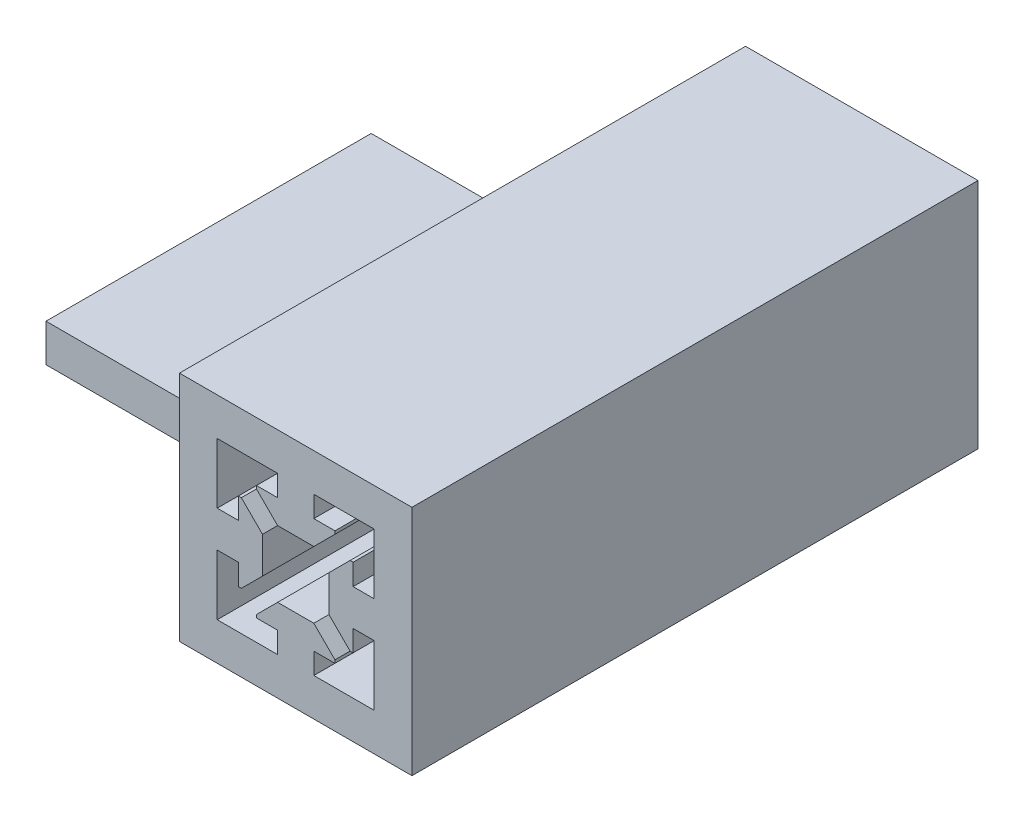
SolidWorks part; units mm, degrees
ref_plane "正面" through (0, 0, 0) normal (0, 0, 1) x (1, 0, 0)
ref_plane "平面" through (0, 0, 0) normal (0, 1, 0) x (1, 0, 0)
ref_plane "右側面" through (0, 0, 0) normal (1, 0, 0) x (0, 0, -1)
sketch "ｽｹｯﾁ1" plane through (0, 0, 0) normal (0, 0, 1) x (1, 0, 0)
  line L0 (40.6, 3) -> (40.6, 33.8) construction
  line L1 (40.6, 3) -> (71.4, 3) construction
  line L2 (71.4, 3) -> (71.4, 33.8) construction
  line L3 (40.6, 33.8) -> (71.4, 33.8) construction
  line L4 (53.6, 26.0027) -> (53.6, 28.8) construction
  line L5 (50.8, 26.0027) -> (53.6, 26.0027) construction
  line L6 (50.8, 25.6027) -> (50.8, 26.0027) construction
  line L7 (53.6, 22.8027) -> (50.8, 25.6027) construction
  line L8 (58.4, 22.8027) -> (53.6, 22.8027) construction
  line L9 (61.2, 25.6027) -> (58.4, 22.8027) construction
  line L10 (61.2, 26.0027) -> (61.2, 25.6027) construction
  line L11 (58.4, 26.0027) -> (61.2, 26.0027) construction
  line L12 (58.4, 26.0027) -> (58.4, 28.8) construction
  line L13 (58.4, 28.8) -> (66.4, 28.8) construction
  line L14 (66.4, 20.8) -> (66.4, 28.8) construction
  line L15 (63.6027, 20.8) -> (66.4, 20.8) construction
  line L16 (63.6027, 23.6) -> (63.6027, 20.8) construction
  line L17 (63.2027, 23.6) -> (63.6027, 23.6) construction
  line L18 (60.4027, 20.8) -> (63.2027, 23.6) construction
  line L19 (60.4027, 16) -> (60.4027, 20.8) construction
  line L20 (63.2027, 13.2) -> (60.4027, 16) construction
  line L21 (63.6027, 13.2) -> (63.2027, 13.2) construction
  line L22 (63.6027, 16) -> (63.6027, 13.2) construction
  line L23 (63.6027, 16) -> (66.4, 16) construction
  line L24 (66.4, 16) -> (66.4, 8) construction
  line L25 (58.4, 8) -> (66.4, 8) construction
  line L26 (58.4, 10.7973) -> (58.4, 8) construction
  line L27 (61.2, 10.7973) -> (58.4, 10.7973) construction
  line L28 (61.2, 11.1973) -> (61.2, 10.7973) construction
  line L29 (58.4, 13.9973) -> (61.2, 11.1973) construction
  line L30 (53.6, 13.9973) -> (58.4, 13.9973) construction
  line L31 (50.8, 11.1973) -> (53.6, 13.9973) construction
  line L32 (50.8, 10.7973) -> (50.8, 11.1973) construction
  line L33 (53.6, 10.7973) -> (50.8, 10.7973) construction
  line L34 (53.6, 10.7973) -> (53.6, 8) construction
  line L35 (53.6, 8) -> (45.6, 8) construction
  line L36 (45.6, 16) -> (45.6, 8) construction
  line L37 (48.3973, 16) -> (45.6, 16) construction
  line L38 (48.3973, 13.2) -> (48.3973, 16) construction
  line L39 (48.7973, 13.2) -> (48.3973, 13.2) construction
  line L40 (51.5973, 16) -> (48.7973, 13.2) construction
  line L41 (51.5973, 20.8) -> (51.5973, 16) construction
  line L42 (48.7973, 23.6) -> (51.5973, 20.8) construction
  line L43 (48.3973, 23.6) -> (48.7973, 23.6) construction
  line L44 (48.3973, 20.8) -> (48.3973, 23.6) construction
  line L45 (48.3973, 20.8) -> (45.6, 20.8) construction
  line L46 (45.6, 20.8) -> (45.6, 28.8) construction
  line L47 (53.6, 28.8) -> (45.6, 28.8) construction
  line L48 (40.6, 3) -> (40.6, 33.8)
  line L49 (40.6, 3) -> (71.4, 3)
  line L50 (71.4, 3) -> (71.4, 33.8)
  line L51 (40.6, 33.8) -> (71.4, 33.8)
  line L52 (53.6, 26.0027) -> (53.6, 28.8)
  line L53 (50.8, 26.0027) -> (53.6, 26.0027)
  line L54 (50.8, 25.6027) -> (50.8, 26.0027)
  line L55 (53.6, 22.8027) -> (50.8, 25.6027)
  line L56 (58.4, 22.8027) -> (53.6, 22.8027)
  line L57 (61.2, 25.6027) -> (58.4, 22.8027)
  line L58 (61.2, 26.0027) -> (61.2, 25.6027)
  line L59 (58.4, 26.0027) -> (61.2, 26.0027)
  line L60 (58.4, 26.0027) -> (58.4, 28.8)
  line L61 (58.4, 28.8) -> (66.4, 28.8)
  line L62 (66.4, 20.8) -> (66.4, 28.8)
  line L63 (63.6027, 20.8) -> (66.4, 20.8)
  line L64 (63.6027, 23.6) -> (63.6027, 20.8)
  line L65 (63.2027, 23.6) -> (63.6027, 23.6)
  line L66 (60.4027, 20.8) -> (63.2027, 23.6)
  line L67 (60.4027, 16) -> (60.4027, 20.8)
  line L68 (63.2027, 13.2) -> (60.4027, 16)
  line L69 (63.6027, 13.2) -> (63.2027, 13.2)
  line L70 (63.6027, 16) -> (63.6027, 13.2)
  line L71 (63.6027, 16) -> (66.4, 16)
  line L72 (66.4, 16) -> (66.4, 8)
  line L73 (58.4, 8) -> (66.4, 8)
  line L74 (58.4, 10.7973) -> (58.4, 8)
  line L75 (61.2, 10.7973) -> (58.4, 10.7973)
  line L76 (61.2, 11.1973) -> (61.2, 10.7973)
  line L77 (58.4, 13.9973) -> (61.2, 11.1973)
  line L78 (53.6, 13.9973) -> (58.4, 13.9973)
  line L79 (50.8, 11.1973) -> (53.6, 13.9973)
  line L80 (50.8, 10.7973) -> (50.8, 11.1973)
  line L81 (53.6, 10.7973) -> (50.8, 10.7973)
  line L82 (53.6, 10.7973) -> (53.6, 8)
  line L83 (53.6, 8) -> (45.6, 8)
  line L84 (45.6, 16) -> (45.6, 8)
  line L85 (48.3973, 16) -> (45.6, 16)
  line L86 (48.3973, 13.2) -> (48.3973, 16)
  line L87 (48.7973, 13.2) -> (48.3973, 13.2)
  line L88 (51.5973, 16) -> (48.7973, 13.2)
  line L89 (51.5973, 20.8) -> (51.5973, 16)
  line L90 (48.7973, 23.6) -> (51.5973, 20.8)
  line L91 (48.3973, 23.6) -> (48.7973, 23.6)
  line L92 (48.3973, 20.8) -> (48.3973, 23.6)
  line L93 (48.3973, 20.8) -> (45.6, 20.8)
  line L94 (45.6, 20.8) -> (45.6, 28.8)
  line L95 (53.6, 28.8) -> (45.6, 28.8)
extrude "ﾎﾞｽ - 押し出し1" add sketch "ｽｹｯﾁ1" along normal blind 75 from offset 13
sketch "ｽｹｯﾁ2" plane through (0, 3, 0) normal (0, -1, 0) x (1, 0, 0)
  circle A1 centre (8, 30) radius 4
sketch "ｽｹｯﾁ3" plane through (40.6, 0, 0) normal (-1, 0, 0) x (0, 0, 1)
  line L1 (65.0862, 8) -> (22, 8)
  line L2 (65.0862, 8) -> (65.0862, 3)
  line L3 (65.0862, 3) -> (22, 3)
  line L4 (22, 8) -> (22, 3)
  line L5 (30, -5) -> (30, 0) construction
  line L6 (88, 3) -> (13, 3) construction
  dimension "D1" = 5
  dimension "D2" = 8
extrude "ﾎﾞｽ - 押し出し2" add sketch "ｽｹｯﾁ3" along normal up to surface (40.6 mm away)
sketch "ｽｹｯﾁ4" plane through (0, 3, 0) normal (0, -1, 0) x (-1, 0, 0)
  line L0 (-40.6, -88) -> (-71.4, -88) construction
  line L1 (-62, -98.7795) -> (-74, -98.7795)
  line L2 (-62, -98.7795) -> (-62, -66.7795)
  line L3 (-62, -66.7795) -> (-74, -66.7795)
  line L4 (-74, -98.7795) -> (-74, -66.7795)
  line L5 (-38, -98.7795) -> (-50, -98.7795)
  line L6 (-38, -98.7795) -> (-38, -66.7795)
  line L7 (-38, -66.7795) -> (-50, -66.7795)
  line L8 (-50, -98.7795) -> (-50, -66.7795)
  line L9 (-62, -98.7795) -> (-50, -98.7795) construction
  point P10 (-56, -88)
  dimension "D1" = 12
  dimension "D2" = 12
  dimension "D3" = 6
  dimension "D4" = 6
  dimension "D5" = 32
sketch "ｽｹｯﾁ5" plane through (0, 3, 0) normal (0, -1, 0) x (-1, 0, 0)
  line L0 (-40.6, -88) -> (-71.4, -88) construction
  line L1 (-38, -23.6572) -> (-74, -23.6572)
  line L2 (-38, -23.6572) -> (-38, -13.6572)
  line L3 (-38, -13.6572) -> (-74, -13.6572)
  line L4 (-74, -23.6572) -> (-74, -13.6572)
  point P9 (-56, -88)
  point P10 (-56, -13.6572)
  dimension "D1" = 36
  dimension "D2" = 10
